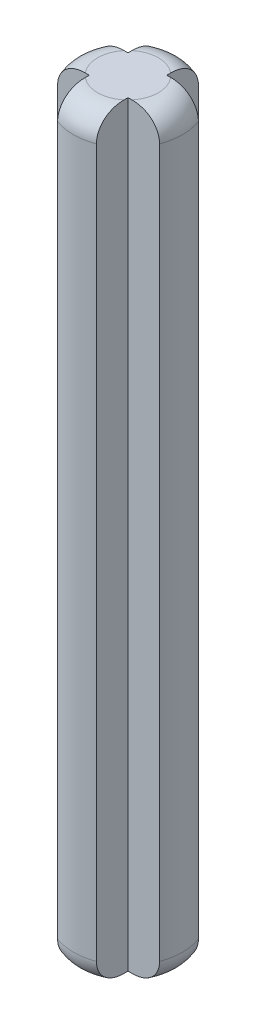
SolidWorks part; units mm, degrees
ref_plane "Front Plane" through (0, 0, 0) normal (0, 0, 1) x (1, 0, 0)
ref_plane "Top Plane" through (0, 0, 0) normal (0, 1, 0) x (1, 0, 0)
ref_plane "Right Plane" through (0, 0, 0) normal (1, 0, 0) x (0, 0, -1)
sketch "Sketch1" plane through (0, 0, 0) normal (0, 1, 0) x (1, 0, 0)
  line L0 (-0.8, -0.8) -> (-0.8, -2.103)
  line L1 (-0.8, 0.8) -> (-2.103, 0.8)
  line L2 (2.103, 0.8) -> (0.8, 0.8)
  line L3 (2.103, -0.8) -> (0.8, -0.8)
  line L4 (0.8, -0.8) -> (0.8, -2.103)
  line L5 (-0.8, -0.8) -> (-2.103, -0.8)
  line L6 (-7.75, 0) -> (-7.75, 0)
  line L7 (-7.75, 0) -> (-7.75, 0)
  line L8 (-0.8, 2.103) -> (-0.8, 0.8)
  line L9 (0.8, 2.103) -> (0.8, 0.8)
  line L10 (-7.75, 0) -> (-7.75, 0)
  line L11 (7.75, 0) -> (7.75, 0)
  line L12 (7.75, 0) -> (7.75, 0)
  line L13 (7.75, 0) -> (7.75, 0)
  line L14 (7.75, 0) -> (7.75, 0)
  line L15 (-7.75, 0) -> (-7.75, 0)
  line L16 (-8.6621, 8.6621) -> (-8.6621, 8.6621)
  line L17 (-8.6621, -8.6621) -> (-8.6621, -8.6621)
  line L18 (-8.6621, -8.6621) -> (-8.6621, -8.6621)
  line L19 (8.6621, -8.6621) -> (8.6621, -8.6621)
  line L20 (8.6621, -8.6621) -> (8.6621, -8.6621)
  line L21 (8.6621, 8.6621) -> (8.6621, 8.6621)
  line L22 (8.6621, 8.6621) -> (8.6621, 8.6621)
  line L23 (-8.6621, 8.6621) -> (-8.6621, 8.6621)
  arc A0 (-2.103, 0.8) -> (-2.103, -0.8) centre (0, 0) ccw
  arc A1 (0.8, 2.103) -> (-0.8, 2.103) centre (0, 0) ccw
  arc A2 (2.103, -0.8) -> (2.103, 0.8) centre (0, 0) ccw
  arc A3 (-0.8, -2.103) -> (0.8, -2.103) centre (0, 0) ccw
  arc A4 (-7.75, 0) -> (-7.75, 0) centre (-7.75, 0) ccw
  arc A5 (-7.75, 0) -> (7.75, 0) centre (0, 0) ccw
  arc A6 (7.75, 0) -> (7.75, 0) centre (7.75, 0) ccw
  arc A7 (7.75, 0) -> (-7.75, 0) centre (0, 0) ccw
  arc A8 (-8.6621, 8.6621) -> (-8.6621, -8.6621) centre (0, 0) ccw
  arc A9 (-8.6621, -8.6621) -> (8.6621, -8.6621) centre (0, 0) ccw
  arc A10 (8.6621, -8.6621) -> (8.6621, 8.6621) centre (0, 0) ccw
  arc A11 (8.6621, 8.6621) -> (-8.6621, 8.6621) centre (0, 0) ccw
  point P26 (0.8, 0)
  dimension "D1" = 4.5
  dimension "D2" = 10
  dimension "D3" = 10
extrude "Boss-Extrude1" add sketch "Sketch1" along normal offset from surface (31.2 mm away) 31.2 contours L0 A3 L4 L3 A2 L2 L9 A1 L8 L1 A0 L5 up to plane "Top Plane"
fillet "Fillet1" radius 1 1 edges at (-2.25, 0, 0)
fillet "Fillet2" radius 1 1 edges at (0, 0, 2.25)
fillet "Fillet3" radius 1 1 edges at (2.25, 0, 0)
fillet "Fillet4" radius 1 1 edges at (0, 0, -2.25)
fillet "Fillet20" radius 1 1 edges at (2.25, 31.2, 0)
fillet "Fillet21" radius 1 1 edges at (0, 31.2, 2.25)
fillet "Fillet22" radius 1 1 edges at (-2.25, 31.2, 0)
fillet "Fillet23" radius 1 1 edges at (0, 31.2, -2.25)
